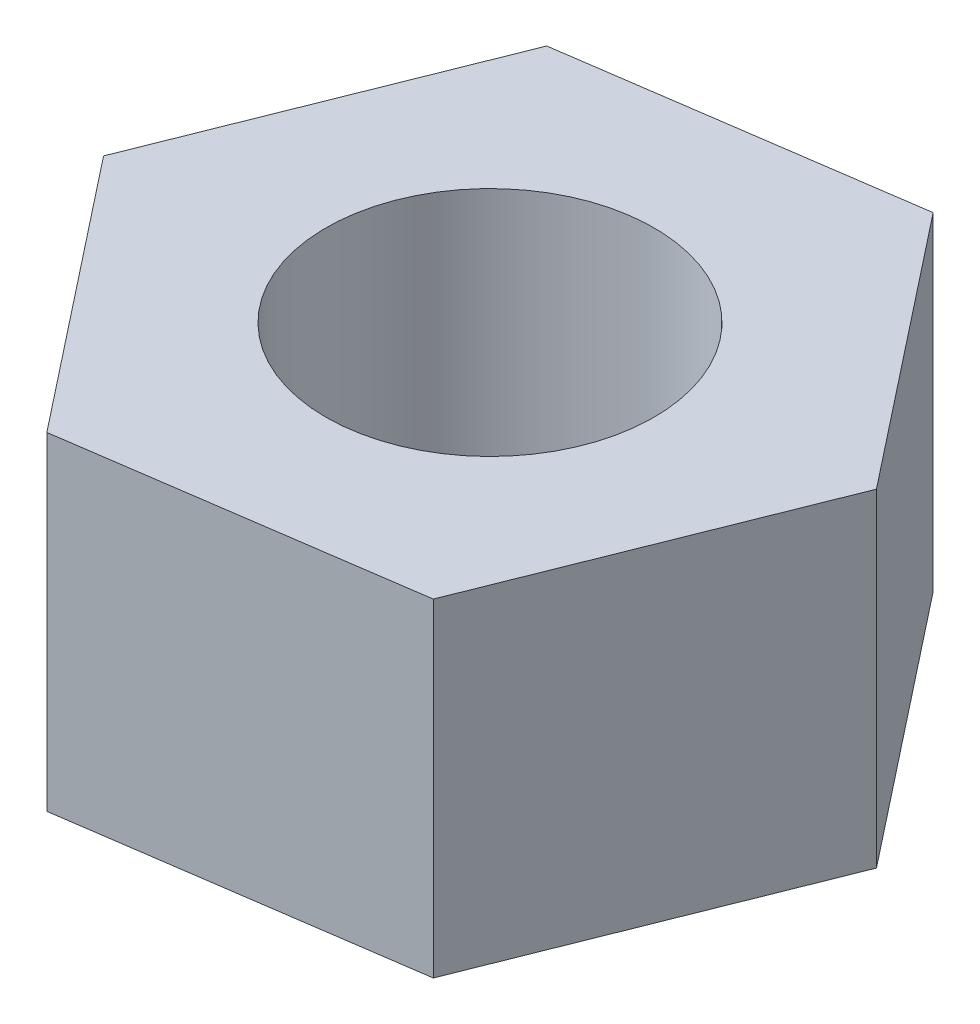
SolidWorks part; units mm, degrees
ref_plane "Front Plane" through (0, 0, 0) normal (0, 0, 1) x (1, 0, 0)
ref_plane "Top Plane" through (0, 0, 0) normal (0, 1, 0) x (1, 0, 0)
ref_plane "Right Plane" through (0, 0, 0) normal (1, 0, 0) x (0, 0, -1)
sketch "Sketch2" plane through (0, 0, 0) normal (0, 1, 0) x (1, 0, 0)
  line L1 (1.9301, -2.4484) -> (3.0854, 0.4473)
  line L2 (3.0854, 0.4473) -> (1.1554, 2.8957)
  line L3 (1.1554, 2.8957) -> (-1.9301, 2.4484)
  line L4 (-1.9301, 2.4484) -> (-3.0854, -0.4473)
  line L5 (-3.0854, -0.4473) -> (-1.1554, -2.8957)
  line L6 (-1.1554, -2.8957) -> (1.9301, -2.4484)
  circle A0 centre (0, 0) radius 2.7 construction
  dimension "D1" = 5.4
extrude "Boss-Extrude1" add sketch "Sketch2" along normal blind 3
sketch "Sketch3" plane through (0, 3, 0) normal (0, 1, 0) x (1, 0, 0)
  circle A0 centre (0, 0) radius 1.5
  dimension "D1" = 3
extrude "Cut-Extrude1" cut sketch "Sketch3" against normal blind 3
